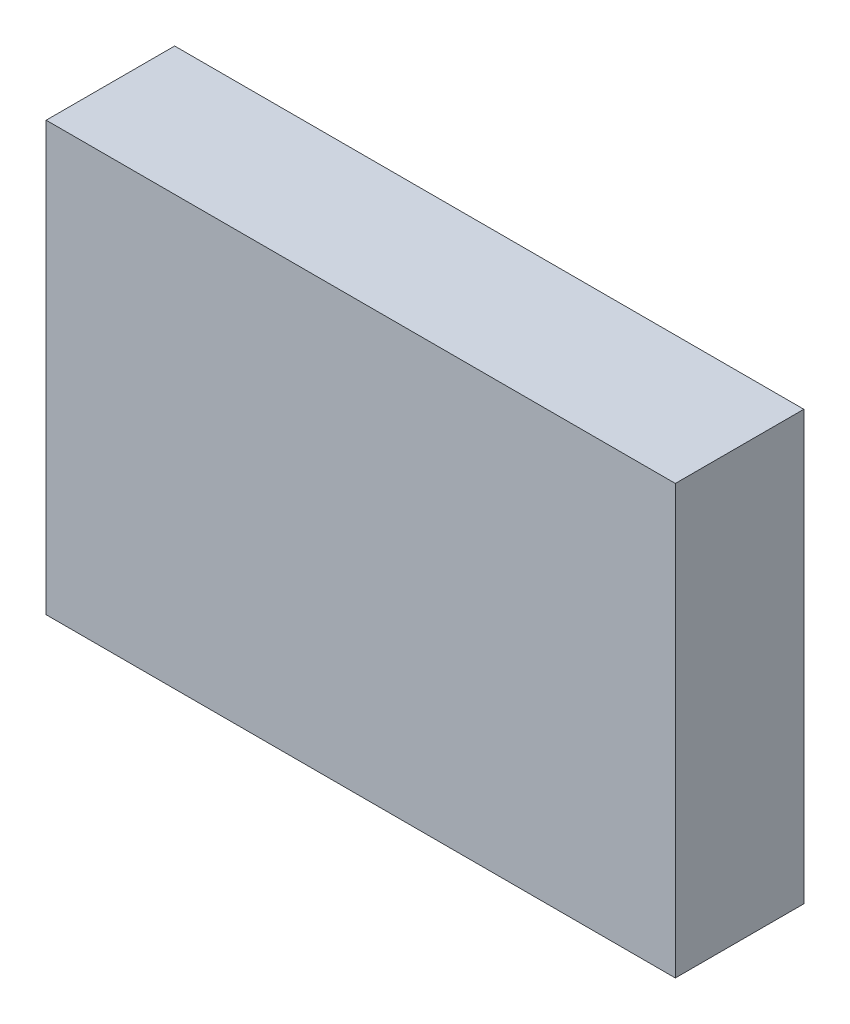
SolidWorks part; units mm, degrees
ref_plane "Plan de face" through (0, 0, 0) normal (0, 0, 1) x (1, 0, 0)
ref_plane "Plan de dessus" through (0, 0, 0) normal (0, 1, 0) x (1, 0, 0)
ref_plane "Plan de droite" through (0, 0, 0) normal (1, 0, 0) x (0, 0, -1)
sketch "Esquisse1" plane through (0, 0, 0) normal (0, 0, 1) x (1, 0, 0)
  line L1 (-42.0874, 23.8367) -> (-27.3974, 23.8367)
  line L2 (-42.0874, 23.8367) -> (-42.0874, 13.8367)
  line L3 (-42.0874, 13.8367) -> (-27.3974, 13.8367)
  line L4 (-27.3974, 23.8367) -> (-27.3974, 13.8367)
  dimension "D1" = 14.69
  dimension "D2" = 10
extrude "Boss.-Extru.1" add sketch "Esquisse1" along normal blind 3
